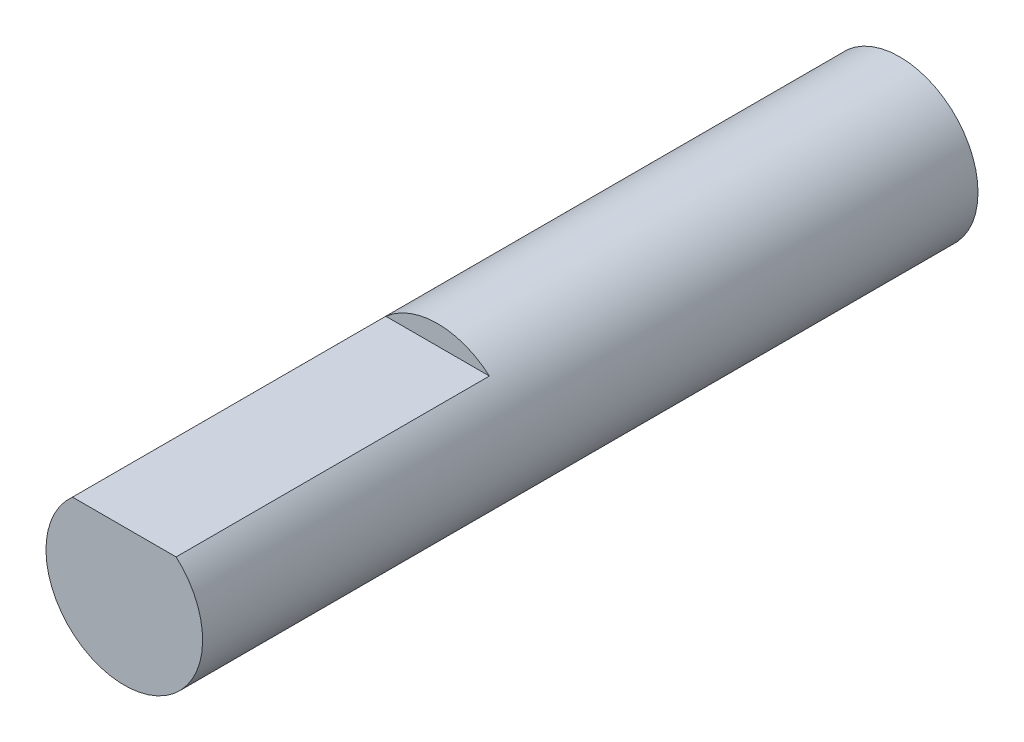
SolidWorks part; units mm, degrees
ref_plane "Front Plane" through (0, 0, 0) normal (0, 0, 1) x (1, 0, 0)
ref_plane "Top Plane" through (0, 0, 0) normal (0, 1, 0) x (1, 0, 0)
ref_plane "Right Plane" through (0, 0, 0) normal (1, 0, 0) x (0, 0, -1)
sketch "Sketch1" plane through (0, 0, 0) normal (0, 0, 1) x (1, 0, 0)
  circle A0 centre (0, 0) radius 2
  dimension "D1" = 4
extrude "Boss-Extrude1" add sketch "Sketch1" along normal blind 19.8
sketch "Sketch2" plane through (0, 0, 19.8) normal (0, 0, 1) x (1, 0, 0)
  line L0 (0, 0) -> (0, 1.5) construction
  line L2 (-1.3229, 1.5) -> (1.3229, 1.5)
  circle A0 centre (0, 0) radius 2 construction
  dimension "D1" = 1.5
extrude "Cut-Extrude1" cut sketch "Sketch2" against normal blind 8 and the other way through all
